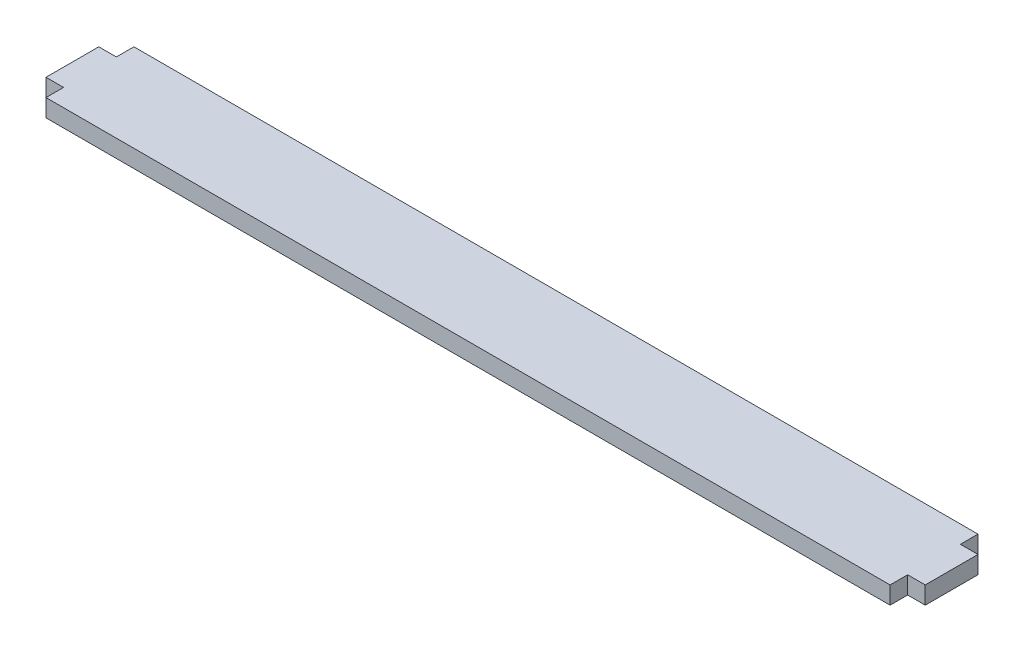
SolidWorks part; units mm, degrees
ref_plane "Front Plane" through (0, 0, 0) normal (0, 0, 1) x (1, 0, 0)
ref_plane "Top Plane" through (0, 0, 0) normal (0, 1, 0) x (1, 0, 0)
ref_plane "Right Plane" through (0, 0, 0) normal (1, 0, 0) x (0, 0, -1)
sketch "Sketch1" plane through (0, 0, 0) normal (0, 1, 0) x (1, 0, 0)
  line L0 (-76.2, -7.9375) -> (76.2, -7.9375)
  line L1 (76.2, -7.9375) -> (76.2, -4.7625)
  line L2 (76.2, -4.7625) -> (79.375, -4.7625)
  line L3 (79.375, -4.7625) -> (79.375, 4.7625)
  line L4 (79.375, 4.7625) -> (76.2, 4.7625)
  line L5 (76.2, 4.7625) -> (76.2, 7.9375)
  line L6 (76.2, 7.9375) -> (-76.2, 7.9375)
  line L7 (-76.2, 7.9375) -> (-76.2, 4.7625)
  line L8 (-76.2, 4.7625) -> (-79.375, 4.7625)
  line L9 (-79.375, 4.7625) -> (-79.375, -4.7625)
  line L10 (-79.375, -4.7625) -> (-76.2, -4.7625)
  line L11 (-76.2, -4.7625) -> (-76.2, -7.9375)
  point P9 (0, 7.9375)
  point P13 (79.375, 0)
  dimension "D1" = 3.175
  dimension "D2" = 9.525
  dimension "D3" = 15.875
  dimension "D4" = 152.4
extrude "Boss-Extrude1" add sketch "Sketch1" along normal blind 3.175
